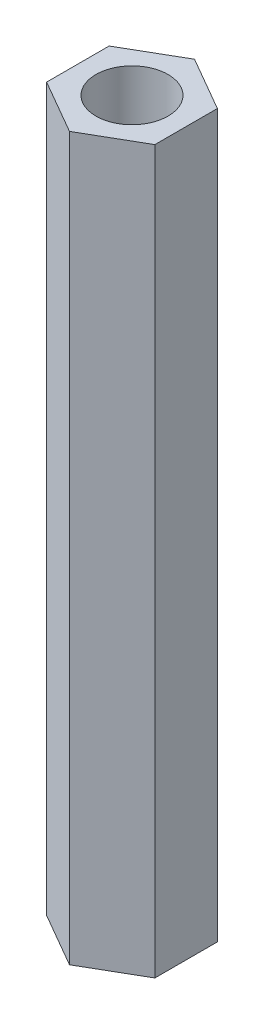
SolidWorks part; units mm, degrees
ref_plane "Front Plane" through (0, 0, 0) normal (0, 0, 1) x (1, 0, 0)
ref_plane "Top Plane" through (0, 0, 0) normal (0, 1, 0) x (1, 0, 0)
ref_plane "Right Plane" through (0, 0, 0) normal (1, 0, 0) x (0, 0, -1)
sketch "Sketch1" plane through (0, 0, 0) normal (0, 1, 0) x (1, 0, 0)
  line L1 (0, -1.7321) -> (1.5, -0.866)
  line L2 (1.5, -0.866) -> (1.5, 0.866)
  line L3 (1.5, 0.866) -> (0, 1.7321)
  line L4 (0, 1.7321) -> (-1.5, 0.866)
  line L5 (-1.5, 0.866) -> (-1.5, -0.866)
  line L6 (-1.5, -0.866) -> (0, -1.7321)
  circle A0 centre (0, 0) radius 1.5 construction
  circle A1 centre (0, 0) radius 1
  dimension "D2" = 2
  dimension "D1" = 3
extrude "Boss-Extrude1" add sketch "Sketch1" along normal blind 20
